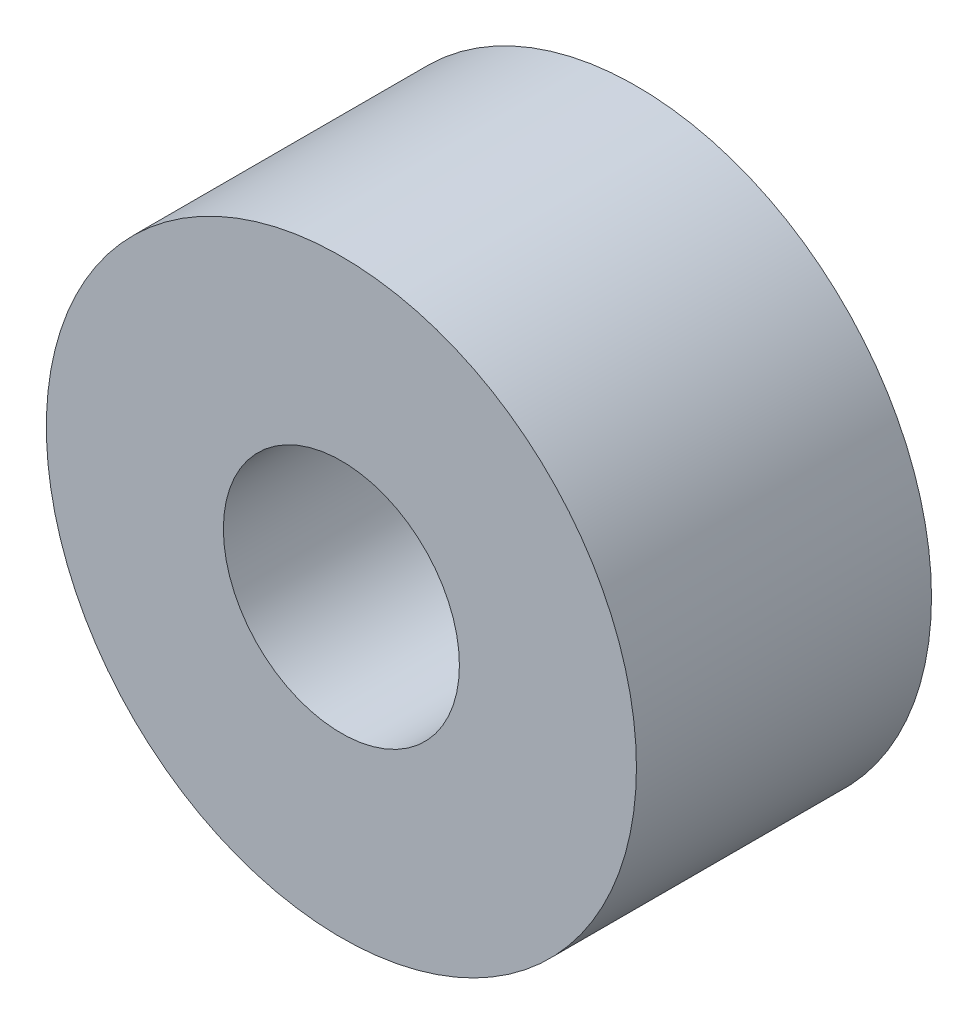
SolidWorks part; units mm, degrees
ref_plane "Alzado" through (0, 0, 0) normal (0, 0, 1) x (1, 0, 0)
ref_plane "Planta" through (0, 0, 0) normal (0, 1, 0) x (1, 0, 0)
ref_plane "Vista lateral" through (0, 0, 0) normal (1, 0, 0) x (0, 0, -1)
sketch "Model" plane through (0, 0, 0) normal (0, 0, 1) x (1, 0, 0)
  circle A0 centre (35.96, 18.8669) radius 2.5
extrude "Saliente-Extruir1" add sketch "Model" along normal blind 2.5
sketch "Croquis1" plane through (0, 0, 2.5) normal (0, 0, 1) x (1, 0, 0)
  circle A0 centre (35.96, 18.8669) radius 1
extrude "Cortar-Extruir1" cut sketch "Croquis1" against normal blind 10
